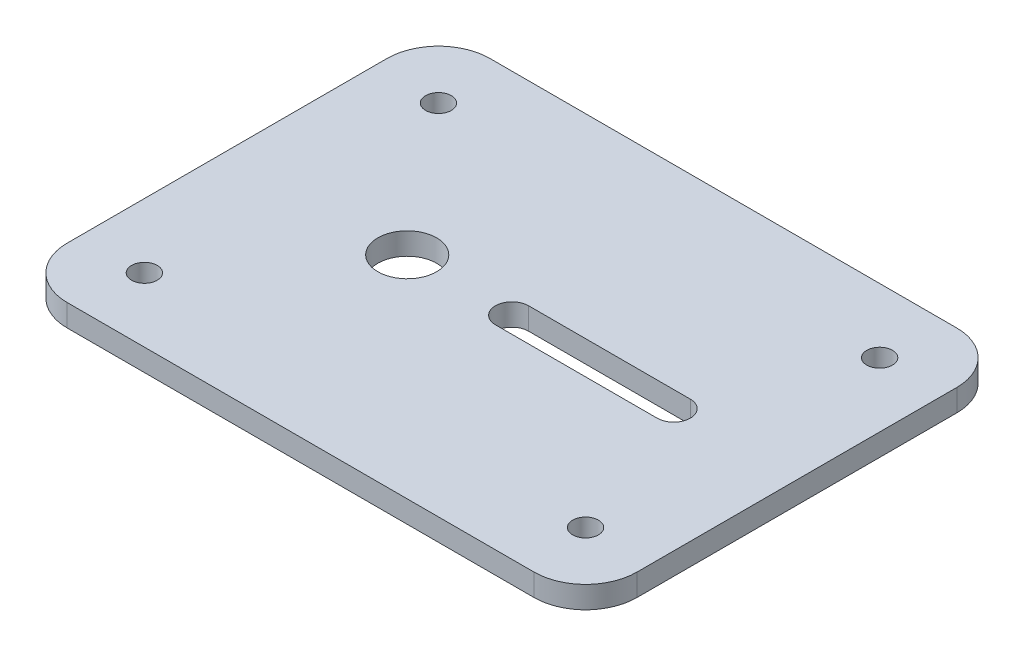
SolidWorks part; units mm, degrees
ref_plane "Спереди" through (0, 0, 0) normal (0, 0, 1) x (1, 0, 0)
ref_plane "Сверху" through (0, 0, 0) normal (0, 1, 0) x (1, 0, 0)
ref_plane "Справа" through (0, 0, 0) normal (1, 0, 0) x (0, 0, -1)
sketch "Эскиз1" plane through (0, 0, 0) normal (0, 1, 0) x (1, 0, 0)
  line L1 (-52.069, -35) -> (52.069, -35)
  line L2 (-52.069, -35) -> (-52.069, 35)
  line L3 (-52.069, 35) -> (52.069, 35)
  line L4 (52.069, -35) -> (52.069, 35)
  line L5 (-52.069, -35) -> (52.069, 35) construction
  line L6 (-52.069, 35) -> (52.069, -35) construction
  point P0 (0, 0)
  dimension "D1" = 70
extrude "Бобышка-Вытянуть1" add sketch "Эскиз1" along normal blind 3
sketch "Эскиз2" plane through (0, 3, 0) normal (0, 1, 0) x (1, 0, 0)
  line L0 (-52.069, 35) -> (-52.069, -35) construction
  line L1 (52.069, 35) -> (-52.069, 35) construction
  circle A0 centre (-43.319, 26.25) radius 1.75
  dimension "D1" = 3.5
  dimension "D3" = 7
  dimension "D2" = 7
extrude "Вырез-Вытянуть1" cut sketch "Эскиз2" against normal blind 10
pattern_linear "Линейный массив1" count 2 spacing 60 along (1, 0, 0) count 2 spacing 40 along (0, 0, 1) of "Вырез-Вытянуть1"
sketch "Эскиз3" plane through (0, 3, 0) normal (0, 1, 0) x (1, 0, 0)
  line L0 (-52.069, -22.5) -> (25.431, -22.5)
  line L1 (-52.069, 35) -> (-52.069, -35) construction
  line L2 (25.431, -22.5) -> (25.431, 35)
  line L3 (52.069, 35) -> (-52.069, 35) construction
  line L4 (25.431, 35) -> (52.069, 35)
  line L5 (52.069, 35) -> (52.069, -35)
  line L6 (52.069, -35) -> (-52.069, -35)
  line L7 (-52.069, -35) -> (-52.069, -22.5)
  circle A0 centre (-43.319, -13.75) radius 1.75 construction
  circle A1 centre (16.681, -13.75) radius 1.75 construction
  dimension "D1" = 7
  dimension "D2" = 7
extrude "Вырез-Вытянуть2" cut sketch "Эскиз3" against normal through all
sketch "Эскиз4" plane through (0, 3, 0) normal (0, 1, 0) x (1, 0, 0)
  line L0 (-13.319, 6.25) -> (8.681, 6.25) construction
  line L1 (-13.319, 8.5) -> (8.681, 8.5)
  line L2 (-13.319, 4) -> (8.681, 4)
  circle A0 centre (-27.569, 6.25) radius 4
  circle A1 centre (-43.319, 26.25) radius 1.75 construction
  arc A2 (-13.319, 8.5) -> (-13.319, 4) centre (-13.319, 6.25) ccw
  arc A3 (8.681, 4) -> (8.681, 8.5) centre (8.681, 6.25) ccw
  point P6 (-2.319, 6.25)
  dimension "D1" = 20
  dimension "D2" = 15.75
  dimension "D3" = 8
  dimension "D5" = 8
  dimension "D6" = 26.5
  dimension "D4" = 4.5
extrude "Вырез-Вытянуть3" cut sketch "Эскиз4" against normal through all
fillet "Скругление1" radius 7 4 edges at (25.431, 1.5, -35) (25.431, 1.5, 22.5) (-52.069, 1.5, -35) (-52.069, 1.5, 22.5)
